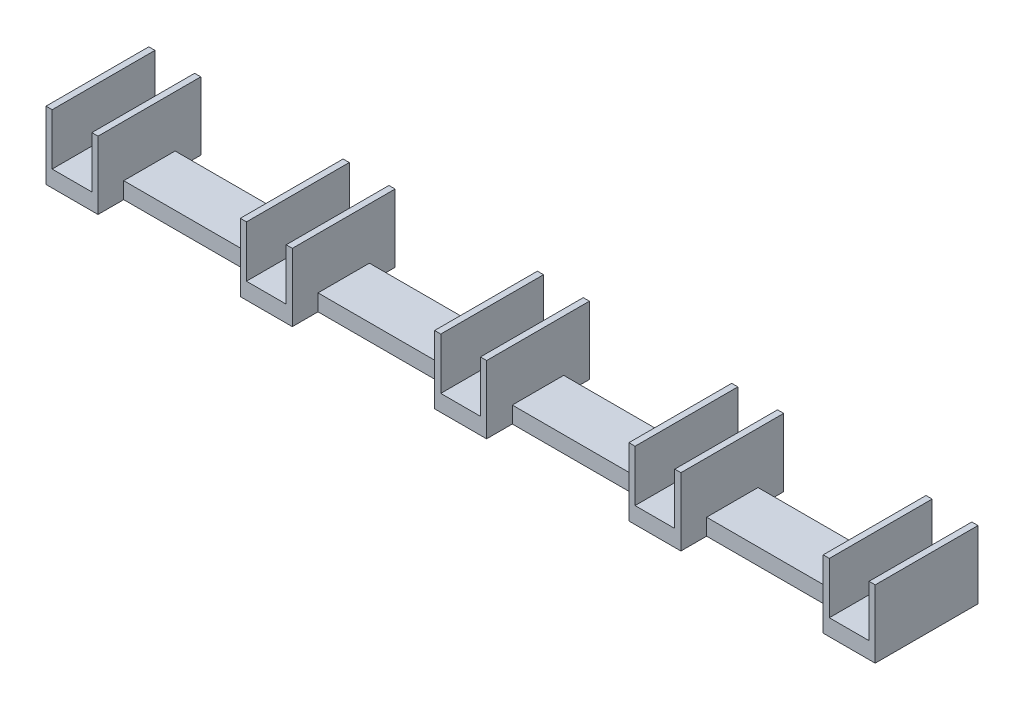
SolidWorks part; units mm, degrees
ref_plane "Ebene vorne" through (0, 0, 0) normal (0, 0, 1) x (1, 0, 0)
ref_plane "Ebene oben" through (0, 0, 0) normal (0, 1, 0) x (1, 0, 0)
ref_plane "Ebene rechts" through (0, 0, 0) normal (1, 0, 0) x (0, 0, -1)
sketch "Skizze1" plane through (0, 0, 0) normal (0, 1, 0) x (1, 0, 0)
  line L0 (7.72, 20) -> (8.92, 20)
  line L1 (0, 0) -> (7.72, 0)
  line L2 (0, 0) -> (0, 20)
  line L3 (0, 20) -> (7.72, 20)
  line L4 (7.72, 0) -> (7.72, 20)
  line L5 (8.92, 20) -> (8.92, 0)
  line L6 (8.92, 0) -> (7.72, 0)
  line L7 (3.86, 0) -> (3.86, 20) construction
  line L8 (0, 20) -> (-1.2, 20)
  line L9 (-1.2, 20) -> (-1.2, 0)
  line L10 (-1.2, 0) -> (0, 0)
  line L11 (7.72, 10) -> (0, 10)
  line L12 (0, 10) -> (7.72, 10)
  line L13 (7.72, 10) -> (160.12, 10)
  line L14 (22.76, 0) -> (22.76, 20) construction
  line L15 (8.92, 0) -> (7.72, 0)
  line L16 (8.92, 20) -> (8.92, 0)
  line L17 (7.72, 20) -> (8.92, 20)
  line L18 (-1.2, 0) -> (0, 0)
  line L19 (-1.2, 20) -> (-1.2, 0)
  line L20 (0, 0) -> (0, 20)
  line L21 (7.72, 0) -> (7.72, 20)
  line L22 (0, 20) -> (-1.2, 20)
  line L23 (41.66, 0) -> (41.66, 20) construction
  line L24 (45.52, 20) -> (46.72, 20)
  line L25 (37.8, 0) -> (37.8, 20)
  line L26 (45.52, 0) -> (45.52, 20)
  line L27 (46.72, 20) -> (46.72, 0)
  line L28 (46.72, 0) -> (45.52, 0)
  line L29 (37.8, 20) -> (36.6, 20)
  line L30 (36.6, 20) -> (36.6, 0)
  line L31 (36.6, 0) -> (37.8, 0)
  line L32 (45.52, 10) -> (37.8, 10)
  line L33 (37.8, 10) -> (45.52, 10)
  line L34 (46.72, 0) -> (45.52, 0)
  line L35 (46.72, 20) -> (46.72, 0)
  line L36 (45.52, 20) -> (46.72, 20)
  line L37 (36.6, 0) -> (37.8, 0)
  line L38 (36.6, 20) -> (36.6, 0)
  line L39 (37.8, 0) -> (37.8, 20)
  line L40 (45.52, 20) -> (37.8, 20)
  line L41 (45.52, 0) -> (45.52, 20)
  line L42 (45.52, 0) -> (37.8, 0)
  line L43 (37.8, 20) -> (36.6, 20)
  line L44 (60.56, 0) -> (60.56, 20) construction
  line L45 (79.46, 0) -> (79.46, 20) construction
  line L46 (83.32, 20) -> (84.52, 20)
  line L47 (75.6, 0) -> (83.32, 0)
  line L48 (75.6, 0) -> (75.6, 20)
  line L49 (75.6, 20) -> (83.32, 20)
  line L50 (83.32, 0) -> (83.32, 20)
  line L51 (84.52, 20) -> (84.52, 0)
  line L52 (84.52, 0) -> (83.32, 0)
  line L53 (75.6, 20) -> (74.4, 20)
  line L54 (74.4, 20) -> (74.4, 0)
  line L55 (74.4, 0) -> (75.6, 0)
  line L56 (83.32, 10) -> (75.6, 10)
  line L57 (75.6, 10) -> (83.32, 10)
  line L58 (84.52, 0) -> (83.32, 0)
  line L59 (84.52, 20) -> (84.52, 0)
  line L60 (83.32, 20) -> (84.52, 20)
  line L61 (74.4, 0) -> (75.6, 0)
  line L62 (74.4, 20) -> (74.4, 0)
  line L63 (75.6, 0) -> (75.6, 20)
  line L64 (83.32, 0) -> (83.32, 20)
  line L65 (75.6, 20) -> (74.4, 20)
  line L66 (98.36, 0) -> (98.36, 20) construction
  line L67 (117.26, 0) -> (117.26, 20) construction
  line L68 (121.12, 20) -> (122.32, 20)
  line L69 (113.4, 0) -> (113.4, 20)
  line L70 (121.12, 0) -> (121.12, 20)
  line L71 (122.32, 20) -> (122.32, 0)
  line L72 (122.32, 0) -> (121.12, 0)
  line L73 (113.4, 20) -> (112.2, 20)
  line L74 (112.2, 20) -> (112.2, 0)
  line L75 (112.2, 0) -> (113.4, 0)
  line L76 (121.12, 10) -> (113.4, 10)
  line L77 (113.4, 10) -> (121.12, 10)
  line L78 (122.32, 0) -> (121.12, 0)
  line L79 (122.32, 20) -> (122.32, 0)
  line L80 (121.12, 20) -> (122.32, 20)
  line L81 (112.2, 0) -> (113.4, 0)
  line L82 (112.2, 20) -> (112.2, 0)
  line L83 (113.4, 0) -> (113.4, 20)
  line L84 (121.12, 20) -> (113.4, 20)
  line L85 (121.12, 0) -> (121.12, 20)
  line L86 (121.12, 0) -> (113.4, 0)
  line L87 (113.4, 20) -> (112.2, 20)
  line L88 (136.16, 0) -> (136.16, 20) construction
  line L89 (155.06, 0) -> (155.06, 20) construction
  line L90 (158.92, 20) -> (160.12, 20)
  line L91 (151.2, 0) -> (158.92, 0)
  line L92 (151.2, 0) -> (151.2, 20)
  line L93 (151.2, 20) -> (158.92, 20)
  line L94 (158.92, 0) -> (158.92, 20)
  line L95 (160.12, 20) -> (160.12, 0)
  line L96 (160.12, 0) -> (158.92, 0)
  line L97 (151.2, 20) -> (150, 20)
  line L98 (150, 20) -> (150, 0)
  line L99 (150, 0) -> (151.2, 0)
  line L100 (158.92, 10) -> (151.2, 10)
  line L101 (151.2, 10) -> (158.92, 10)
  line L102 (160.12, 0) -> (158.92, 0)
  line L103 (160.12, 20) -> (160.12, 0)
  line L104 (158.92, 20) -> (160.12, 20)
  line L105 (150, 0) -> (151.2, 0)
  line L106 (150, 20) -> (150, 0)
  line L107 (151.2, 0) -> (151.2, 20)
  line L108 (158.92, 0) -> (158.92, 20)
  line L109 (151.2, 20) -> (150, 20)
  line L110 (8.92, 15) -> (36.6, 15)
  line L111 (8.92, 5) -> (36.6, 5)
  line L112 (74.4, 5) -> (46.72, 5)
  line L113 (74.4, 15) -> (46.72, 15)
  line L114 (150, 5) -> (122.32, 5)
  line L115 (84.52, 5) -> (112.2, 5)
  line L116 (84.52, 15) -> (112.2, 15)
  line L117 (150, 15) -> (122.32, 15)
  point P19 (3.86, 10)
  point P31 (41.66, 10)
  point P47 (79.46, 10)
  point P62 (117.26, 10)
  point P77 (155.06, 10)
  point P80 (22.76, 5)
  point P81 (22.76, 15)
  dimension "D1" = 7.72
  dimension "D2" = 20
  dimension "D3" = 1.2
  dimension "D4" = 18.9
  dimension "D6" = 5
extrude "Aufsatz-Linear austragen5" add sketch "Skizze1" along normal blind 3.2 contours L11 L4 L3 L2 | L9 L10 L2 L8 | L4 L11 L2 L1 | L4 L13 L16 L5 L0 | L13 L4 L6 L16 L5 | L110 L16 L13 L38 | L5 L111 L30 L13 | L29 L30 L38 L13 L25 | L30 L38 L31 L25 L13 | L26 L40 L25 L13 | L27 L24 L26 L13 L35 | L28 L35 L27 L13 L26 | L42 L26 L13 L25 | L62 L113 L35 L13 | L112 L54 L13 L27 | L13 L50 L49 L48 | L53 L54 L62 L13 L48 | L54 L62 L55 L48 L13 | L47 L50 L13 L48 | L51 L46 L50 L13 L59 | L52 L59 L51 L13 L50 | L116 L59 L13 L82 | L51 L115 L74 L13 | L70 L84 L69 L13 | L73 L74 L82 L13 L69 | L74 L82 L75 L69 L13 | L71 L68 L70 L13 L79 | L86 L70 L13 L69 | L72 L79 L71 L13 L70 | L106 L117 L79 L13 | L114 L98 L13 L71 | L97 L98 L106 L13 L92 | L98 L106 L99 L92 L13 | L13 L94 L93 L92 | L95 L90 L94 L13 | L91 L94 L13 L92 | L96 L95 L13 L94
sketch "Skizze2" plane through (0, 3.2, 0) normal (0, 1, 0) x (1, 0, 0)
  line L1 (8.92, 0) -> (7.72, 0)
  line L2 (8.92, 0) -> (8.92, 20)
  line L3 (8.92, 20) -> (7.72, 20)
  line L4 (7.72, 0) -> (7.72, 20)
  line L5 (-1.2, 0) -> (0, 0)
  line L6 (-1.2, 0) -> (-1.2, 20)
  line L7 (-1.2, 20) -> (0, 20)
  line L8 (0, 0) -> (0, 20)
  line L9 (36.6, 0) -> (37.8, 0)
  line L10 (36.6, 0) -> (36.6, 20)
  line L11 (36.6, 20) -> (37.8, 20)
  line L12 (37.8, 0) -> (37.8, 20)
  line L13 (45.52, 20) -> (46.72, 20)
  line L14 (45.52, 20) -> (45.52, 0)
  line L15 (45.52, 0) -> (46.72, 0)
  line L16 (46.72, 20) -> (46.72, 0)
  line L17 (74.4, 20) -> (75.6, 20)
  line L18 (74.4, 20) -> (74.4, 0)
  line L19 (74.4, 0) -> (75.6, 0)
  line L20 (75.6, 20) -> (75.6, 0)
  line L21 (83.32, 0) -> (84.52, 0)
  line L22 (83.32, 0) -> (83.32, 20)
  line L23 (83.32, 20) -> (84.52, 20)
  line L24 (84.52, 0) -> (84.52, 20)
  line L25 (112.2, 20) -> (113.4, 20)
  line L26 (112.2, 20) -> (112.2, 0)
  line L27 (112.2, 0) -> (113.4, 0)
  line L28 (113.4, 20) -> (113.4, 0)
  line L29 (121.12, 0) -> (122.32, 0)
  line L30 (121.12, 0) -> (121.12, 20)
  line L31 (121.12, 20) -> (122.32, 20)
  line L32 (122.32, 0) -> (122.32, 20)
  line L33 (150, 20) -> (151.2, 20)
  line L34 (150, 20) -> (150, 0)
  line L35 (150, 0) -> (151.2, 0)
  line L36 (151.2, 20) -> (151.2, 0)
  line L37 (158.92, 0) -> (160.12, 0)
  line L38 (158.92, 0) -> (158.92, 20)
  line L39 (158.92, 20) -> (160.12, 20)
  line L40 (160.12, 0) -> (160.12, 20)
extrude "Aufsatz-Linear austragen6" add sketch "Skizze2" along normal blind 10
